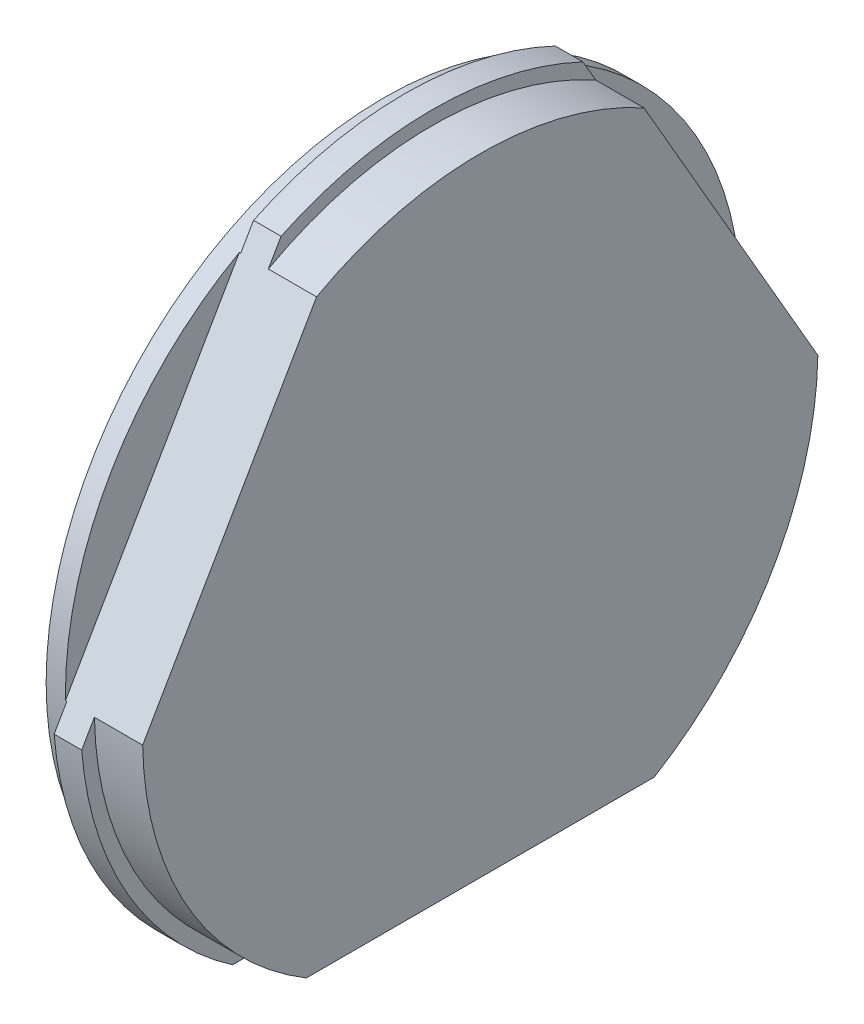
SolidWorks part; units mm, degrees
ref_plane "Спереди" through (0, 0, 0) normal (0, 0, 1) x (1, 0, 0)
ref_plane "Сверху" through (0, 0, 0) normal (0, 1, 0) x (1, 0, 0)
ref_plane "Справа" through (0, 0, 0) normal (1, 0, 0) x (0, 0, -1)
sketch "Эскиз1" plane through (0, 0, 0) normal (0, 0, 1) x (1, 0, 0)
  line L0 (-6.565, 0) -> (7.9071, 0) construction
  line L2 (-1.5, 24.5) -> (-1.5, 20)
  line L3 (-1.5, 24.5) -> (0, 24.5)
  line L4 (0, 24.5) -> (0, 25.5)
  line L5 (0, 25.5) -> (2, 25.5)
  line L6 (2, 25.5) -> (2, 24.5)
  line L7 (2, 24.5) -> (5.5, 24.5)
  line L8 (5.5, 24.5) -> (5.5, 0)
  line L9 (5.5, 0) -> (4, 0)
  line L10 (-1.5, 20) -> (4, 20)
  line L11 (4, 20) -> (4, 0)
  dimension "D1" = 51
  dimension "D2" = 49
  dimension "D3" = 49
  dimension "D4" = 1.5
  dimension "D5" = 7
  dimension "D6" = 2
  dimension "D7" = 5.5
  dimension "D8" = 40
revolve "Повернуть1" add sketch "Эскиз1" angle 360 about L0
sketch "Эскиз2" plane through (2, 0, 0) normal (1, 0, 0) x (0, 0, -1)
  line L0 (-25.4193, -2.0275) -> (-10.9538, 23.0275)
  line L1 (10.9538, 23.0275) -> (25.4193, -2.0275)
  line L2 (-14.4655, -21) -> (14.4655, -21)
  circle A0 centre (0, 0) radius 25.5 construction
  circle M6 centre (0, 0) radius 25.5
  circle M7 centre (0, 0) radius 24.5
  dimension "D1" = 60
  dimension "D2" = 60
  dimension "D3" = 21
extrude "Вырез-Вытянуть1" cut sketch "Эскиз2" against normal offset from surface 0.1 and the other way through all contours L0 M6 M7 | L0 M7 | L2 M7 | L2 M6 M7 | L1 M7 | L1 M6 M7 up to face at (0, 0, 24.5) offset beyond the face yes
